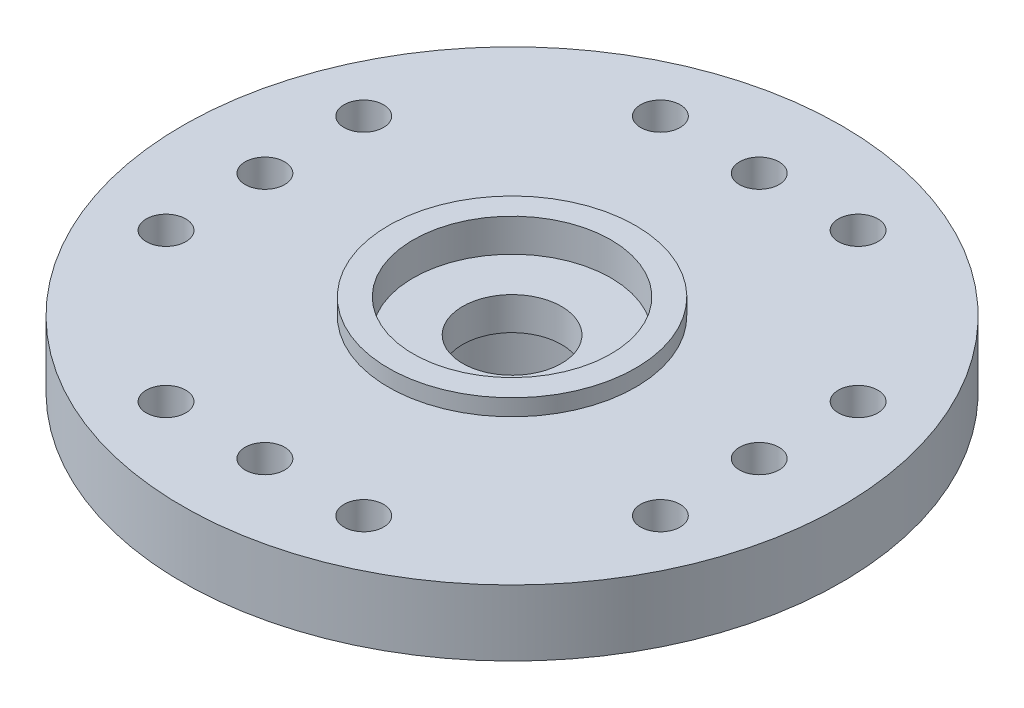
SolidWorks part; units mm, degrees
material "PVC rigide"
ref_plane "Plan de face" through (0, 0, 0) normal (0, 0, 1) x (1, 0, 0)
ref_plane "Plan de dessus" through (0, 0, 0) normal (0, 1, 0) x (1, 0, 0)
ref_plane "Plan de droite" through (0, 0, 0) normal (1, 0, 0) x (0, 0, -1)
sketch "Esquisse1" plane through (0, 0, 0) normal (0, 0, 1) x (1, 0, 0)
  line L0 (0, 0) -> (0, 5) construction
  line L1 (2.75, 0) -> (2.75, 3)
  line L2 (2.75, 3) -> (1.5, 3)
  line L3 (1.5, 3) -> (1.5, 4)
  line L4 (1.5, 4) -> (3, 4)
  line L5 (3, 4) -> (3, 5)
  line L6 (3, 5) -> (3.75, 5)
  line L7 (3.75, 5) -> (3.75, 4.5)
  line L8 (3.75, 4.5) -> (10, 4.5)
  line L9 (10, 4.5) -> (10, 2.5)
  line L10 (10, 2.5) -> (4.5, 2.5)
  line L11 (4.5, 2.5) -> (4.5, 0)
  line L12 (4.5, 0) -> (2.75, 0)
  dimension "D1" = 6
  dimension "D2" = 7.5
  dimension "D3" = 3
  dimension "D4" = 5.5
  dimension "D5" = 9
  dimension "D6" = 20
  dimension "D7" = 0.5
  dimension "D8" = 2
  dimension "D9" = 2.5
  dimension "D10" = 3
  dimension "D11" = 1
revolve "Révolution1" add sketch "Esquisse1" angle 360 about L0
sketch "Sketch1" plane through (0, 4.5, 0) normal (0, 1, 0) x (1, 0, 0)
  line L0 (0, 10) -> (0, -10) construction
  line L1 (-2.592, 7.5) -> (3, 7.5) construction
  circle A0 centre (0, 0) radius 10 construction
  circle A1 centre (0, 7.5) radius 0.6
  circle A2 centre (3, 7.5) radius 0.6
  circle A3 centre (-3, 7.5) radius 0.6
  dimension "D2" = 1.2
  dimension "D4" = 1.2
  dimension "D1" = 2.5
  dimension "D3" = 3
extrude "Cut-Extrude1" cut sketch "Sketch1" against normal up to surface (2 mm away) up to face at (0, 2.5, -10)
pattern_circular "CirPattern1" count 4 every 90 about axis through (0, 0, 0) along (0, 1, 0) of "Cut-Extrude1"
